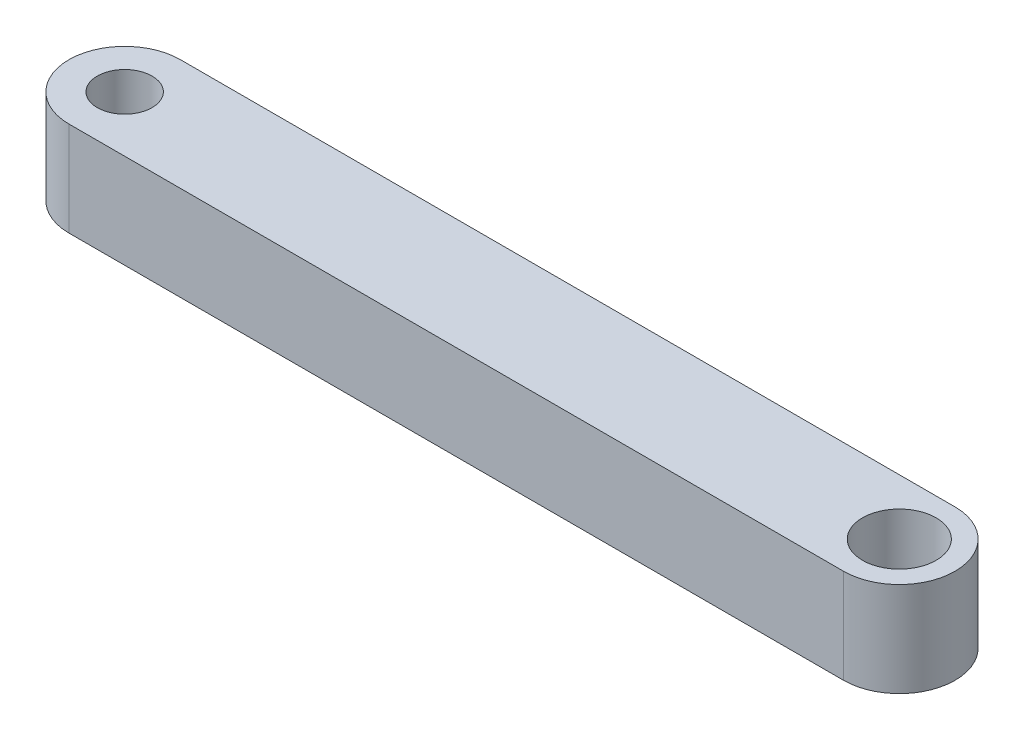
SolidWorks part; units mm, degrees
ref_plane "Front Plane" through (0, 0, 0) normal (0, 0, 1) x (1, 0, 0)
ref_plane "Top Plane" through (0, 0, 0) normal (0, 1, 0) x (1, 0, 0)
ref_plane "Right Plane" through (0, 0, 0) normal (1, 0, 0) x (0, 0, -1)
ref_plane "Plane1" through (0, 0, 0) normal (0, -1, 0) x (1, 0, 0)
sketch "Sketch1" plane through (0, 0, 0) normal (0, -1, 0) x (1, 0, 0)
  line L0 (32, 2.95) -> (-9, 2.95)
  line L1 (-9, -2.95) -> (32, -2.95)
  line L3 (32, 0) -> (31.9997, -0.0002) construction
  line L4 (32, 0) -> (32.0173, -0.0096) construction
  line L5 (32, 0) -> (32.0096, 0.0173) construction
  line L7 (32, 0) -> (32.0001, -0.0001) construction
  arc A0 (-9, 2.95) -> (-9, -2.95) centre (-9, 0) ccw
  arc A1 (32, -2.95) -> (32, 2.95) centre (32, 0) ccw
  circle A2 centre (32, 0) radius 1.95
  circle A3 centre (-9, 0) radius 1.45
  point P9 (-11.95, 0)
  point P10 (34.95, 0)
  point P22 (53.2116, 8.66)
  dimension "D1" = 2.9
  dimension "D2" = 3.9
  dimension "D3" = 2.95
  dimension "D4" = 41
  dimension "D5" = 9
extrude "Boss-Extrude1" add sketch "Sketch1" against normal blind 5
